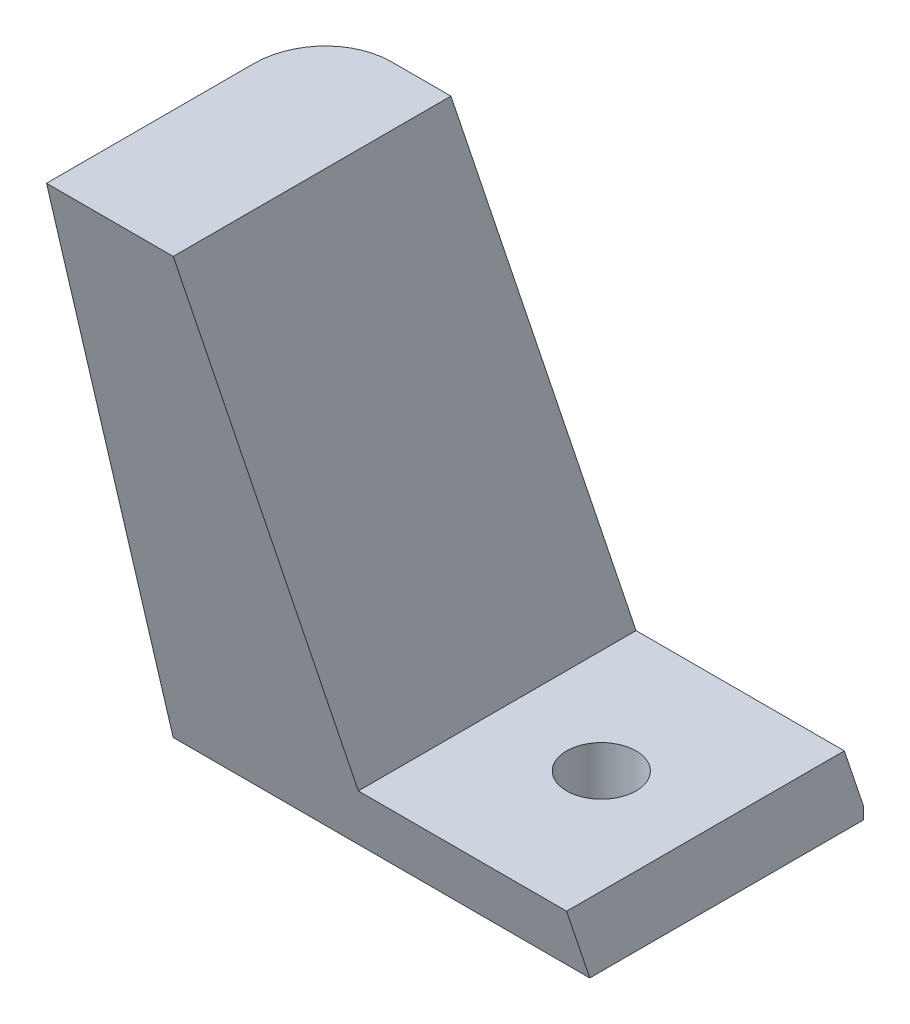
SolidWorks part; units mm, degrees
ref_plane "Спереди" through (0, 0, 0) normal (0, 0, 1) x (1, 0, 0)
ref_plane "Сверху" through (0, 0, 0) normal (0, 1, 0) x (1, 0, 0)
ref_plane "Справа" through (0, 0, 0) normal (1, 0, 0) x (0, 0, -1)
sketch "Эскиз1" plane through (0, 0, 0) normal (0, 1, 0) x (1, 0, 0)
  line L1 (-82.6594, 0) -> (83.4888, 0) construction
  line L3 (-45, 0) -> (-45, 45)
  line L4 (-45, 45) -> (45, 45)
  line L5 (45, 45) -> (45, -45)
  line L6 (45, -45) -> (-45, -45)
  line L7 (-45, -45) -> (-45, 0)
  dimension "D1" = 90
  dimension "D2" = 90
  dimension "D4" = 45
sketch "Эскиз2" plane through (0, 0, 0) normal (0, 0, 1) x (1, 0, 0)
  line L0 (-45, 0) -> (-30, 0)
  line L1 (-30, 0) -> (-30, 45)
  line L2 (45, 0) -> (-45, 0) construction
  line L4 (-45, 0) -> (-30, 0)
  line L5 (0, 0) -> (0, 57.5371) construction
  line L6 (-39.125, 45) -> (-30, 45)
  line L7 (0, 45) -> (-39.125, 45)
  line L8 (-39.125, 45) -> (-45, 0)
  dimension "D1" = 45
  dimension "D2" = 39.125
  dimension "D3" = 82.562
  dimension "D4" = 15
  dimension "D5" = 45
sketch "Эскиз4" plane through (0, 0, 0) normal (1, 0, 0) x (0, 0, -1)
  line L0 (-50.289, 0) -> (-50, 45)
  line L1 (-35.289, 45) -> (-50, 45)
  line L2 (0, 0) -> (30.289, 0)
  line L3 (-15.2933, 45) -> (-35.289, 45)
  line L4 (-50.289, 0) -> (-35.289, 45)
  line L5 (-50.289, 0) -> (-30.289, 0)
  line L6 (-30.289, 0) -> (-15.2933, 45)
  line L7 (-15.2933, 45) -> (15.2933, 45)
  line L8 (0, 45) -> (0, 0)
  line L9 (0, 0) -> (-30.289, 0)
  line L10 (30.289, 0) -> (15.2933, 45)
  line L11 (50.289, 0) -> (30.289, 0)
  line L12 (50.289, 0) -> (35.289, 45)
  line L13 (15.2933, 45) -> (35.289, 45)
  line L14 (35.289, 45) -> (50, 45)
  line L15 (50.289, 0) -> (50, 45)
  line L16 (0, 45) -> (15.2933, 45)
  dimension "D1" = 71.565
  dimension "D2" = 71.57
  dimension "D3" = 19.9957
  dimension "D4" = 45
  dimension "D5" = 20
  dimension "D6" = 50
  dimension "D7" = 30.289
  dimension "D8" = 45
extrude "Бобышка-Вытянуть8" add sketch "Эскиз2" against normal blind 50 contours L6 L8 L0 L1
extrude "Вырез-Вытянуть3" cut sketch "Эскиз4" against normal blind 60 contours L12 L15 L14 | L2 L10 L7 L8
sketch "Эскиз5" plane through (-30, 0, 0) normal (1, 0, 0) x (0, 0, -1)
  line L0 (50, 0) -> (50, 0.8669)
  line L2 (50, 0.8669) -> (48.6223, 5)
  line L3 (50, 0.8669) -> (35.289, 45) construction
  line L4 (48.6223, 5) -> (28.6228, 5)
  line L5 (30.289, 0) -> (15.2933, 45) construction
  line L6 (28.6228, 5) -> (30.289, 0)
  line L7 (30.289, 0) -> (50, 0)
  dimension "D1" = 19.9995
extrude "Бобышка-Вытянуть5" add sketch "Эскиз5" along normal blind 15
sketch "Эскиз6" plane through (0, 5, 0) normal (0, 1, 0) x (1, 0, 0)
  line L0 (-15, 38.6225) -> (-30, 38.6225) construction
  line L1 (-15, 48.6223) -> (-15, 28.6228) construction
  line L2 (-30, 48.6223) -> (-30, 28.6228) construction
  line L3 (-22.5, 48.6223) -> (-22.5, 28.6228) construction
  line L4 (-15, 48.6223) -> (-30, 48.6223) construction
  line L5 (-15, 28.6228) -> (-30, 28.6228) construction
  circle A0 centre (-22.5, 38.6225) radius 2.5
  dimension "D1" = 5
extrude "Вырез-Вытянуть4" cut sketch "Эскиз6" against normal blind 15
fillet "Скругление3" radius 5 2 edges at (-44.9434, 0.4335, -50) (-42.0059, 22.9335, -42.6445)
